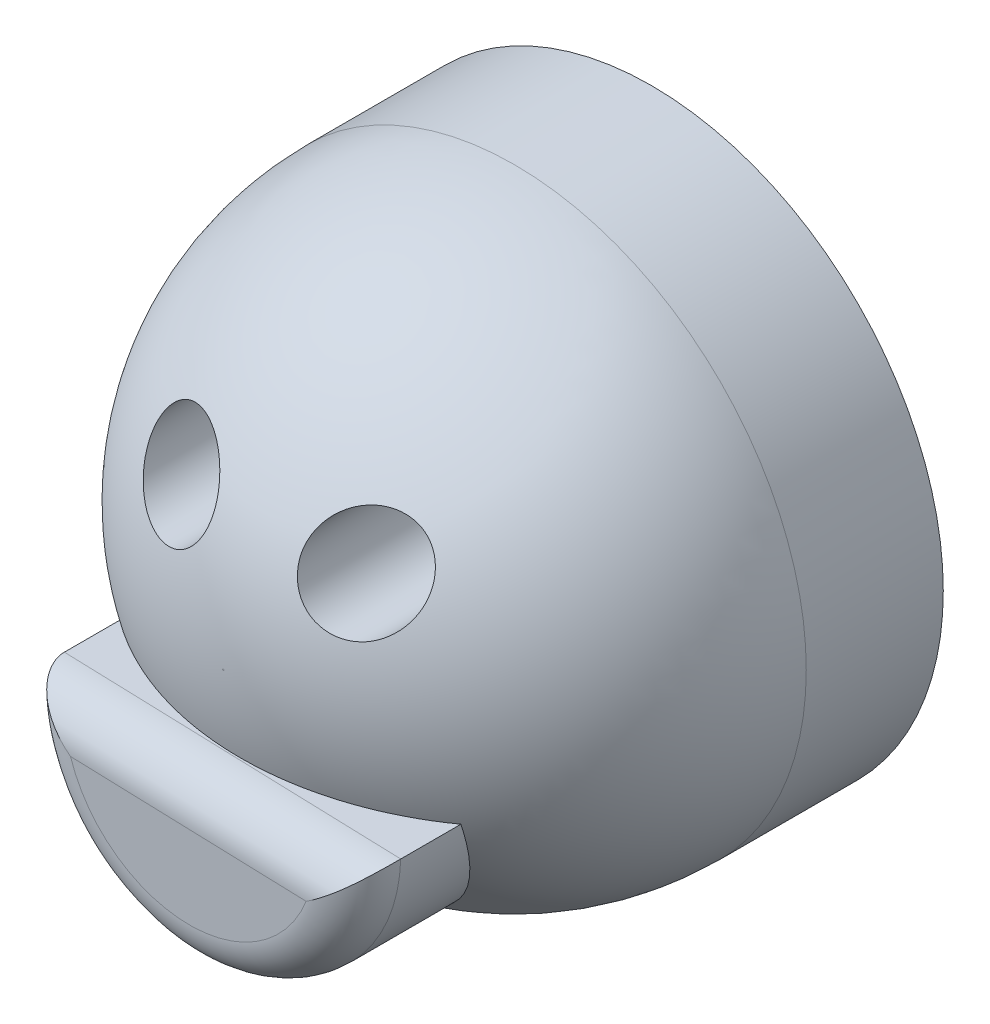
SolidWorks part; units mm, degrees
ref_plane "Front Plane" through (0, 0, 0) normal (0, 0, 1) x (1, 0, 0)
ref_plane "Top Plane" through (0, 0, 0) normal (0, 1, 0) x (1, 0, 0)
ref_plane "Right Plane" through (0, 0, 0) normal (1, 0, 0) x (0, 0, -1)
sketch "Sketch1" plane through (0, 0, 0) normal (0, 0, 1) x (1, 0, 0)
  circle A0 centre (0, 0) radius 34.075
  dimension "D1" = 68.15
extrude "Boss-Extrude1" add sketch "Sketch1" along normal blind 50
fillet "Fillet1" radius 34 1 edges at (34.075, 0, 50)
sketch "Sketch2" [suppressed] plane through (0, 0, 0) normal (0, 0, -1) x (-1, 0, 0)
  spline S0 degree 3 poles (10.0174, 7.2867) (1.4961, 11.0299) (10.5394, 15.5378) (19.3865, 9.6879) (10.0174, 7.2867) (1.4961, 11.0299) (10.5394, 15.5378) knots -0.755957 -0.487243 -0.239087 0 0.244043 0.512757 0.760913 1 1.244043 1.512757 1.760913 only from (4.3557, 11.1083) to (4.3557, 11.1083)
  spline S1 degree 3 poles (-10.5862, 7.8689) (-19.1076, 11.6122) (-10.0642, 16.12) (-1.2171, 10.2702) (-10.5862, 7.8689) (-19.1076, 11.6122) (-10.0642, 16.12) knots -0.755957 -0.487243 -0.239087 0 0.244043 0.512757 0.760913 1 1.244043 1.512757 1.760913 only from (-16.248, 11.6906) to (-16.248, 11.6906)
sketch "Sketch3" plane through (0, 0, 0) normal (0, 0, -1) x (-1, 0, 0)
  circle A0 centre (-11.4272, 12.8505) radius 5.5
  circle A1 centre (9.2574, 12.8505) radius 5.5
  dimension "D1" = 11
  dimension "D2" = 11
extrude "Cut-Extrude1" cut sketch "Sketch3" against normal blind 57
sketch "Sketch4" plane through (0, 0, 0) normal (0, 0, -1) x (-1, 0, 0)
  line L0 (-19.7214, -9.7757) -> (19.5559, -8.5017)
  arc A0 (-19.7214, -9.7757) -> (19.5559, -8.5017) centre (-0.0828, -9.1387) ccw
extrude "Boss-Extrude2" add sketch "Sketch4" against normal blind 54
fillet "Fillet2" radius 5 2 edges at (0.0828, -9.1387, 54) (-0.5543, -28.7773, 54)
sketch "Sketch5" plane through (0, 0, 0) normal (0, 0, -1) x (-1, 0, 0)
  circle A0 centre (0, 0) radius 28.2539
  point P2 (0, 0)
extrude "Cut-Extrude2" cut sketch "Sketch5" against normal blind 27
